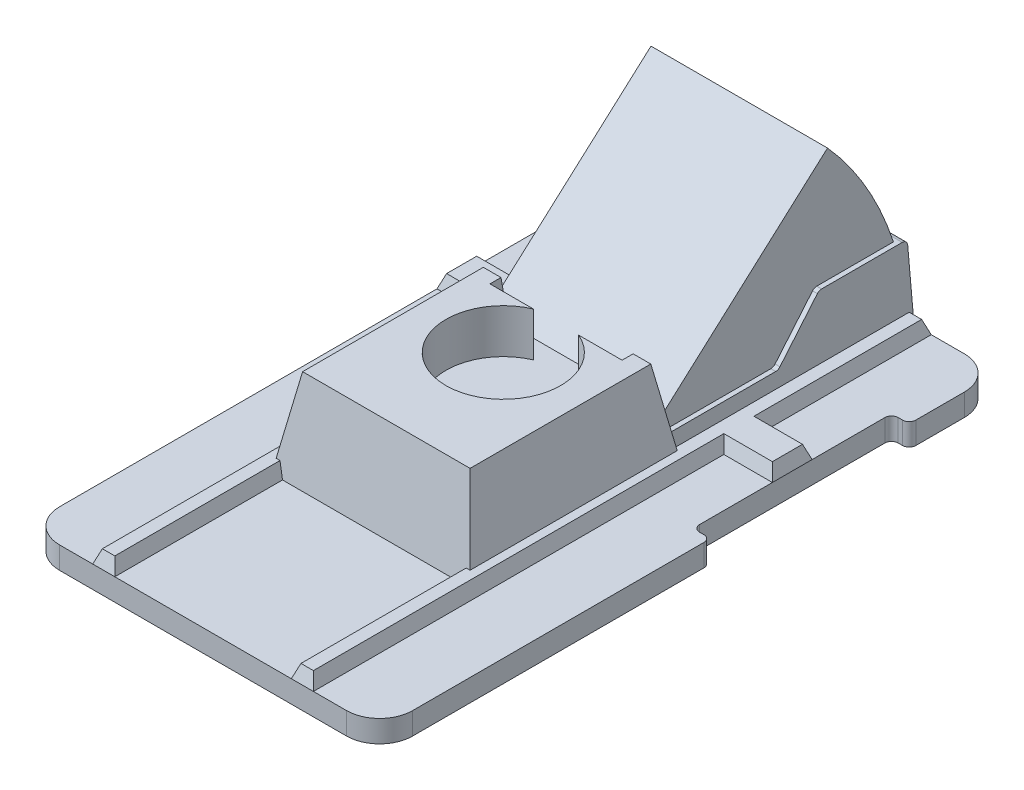
SolidWorks part; units mm, degrees
ref_plane "Front Plane" through (0, 0, 0) normal (0, 0, 1) x (1, 0, 0)
ref_plane "Top Plane" through (0, 0, 0) normal (0, 1, 0) x (1, 0, 0)
ref_plane "Right Plane" through (0, 0, 0) normal (1, 0, 0) x (0, 0, -1)
sketch "Sketch1" plane through (0, 0, 0) normal (0, 1, 0) x (1, 0, 0)
  line L0 (8, 10.3) -> (8, 12.5)
  line L1 (6.5, -14) -> (-6.5, -14)
  line L2 (8, -12.5) -> (8, 0.7)
  line L3 (6.5, 14) -> (-6.5, 14)
  line L4 (-8, -12.5) -> (-8, 12.5)
  line L5 (8, -14) -> (-8, 14) construction
  line L6 (8, 14) -> (-8, -14) construction
  line L7 (7.7, 10) -> (7.5, 10)
  line L9 (7.7, 1) -> (7.5, 1)
  line L10 (7.2, 9.7) -> (7.2, 1.3)
  arc A0 (-6.5, -14) -> (-8, -12.5) centre (-6.5, -12.5) cw
  arc A1 (6.5, -14) -> (8, -12.5) centre (6.5, -12.5) ccw
  arc A2 (8, 12.5) -> (6.5, 14) centre (6.5, 12.5) ccw
  arc A3 (-6.5, 14) -> (-8, 12.5) centre (-6.5, 12.5) ccw
  arc A4 (8, 0.7) -> (7.7, 1) centre (7.7, 0.7) ccw
  arc A5 (7.5, 1) -> (7.2, 1.3) centre (7.5, 1.3) cw
  arc A6 (7.7, 10) -> (8, 10.3) centre (7.7, 10.3) ccw
  arc A7 (7.5, 10) -> (7.2, 9.7) centre (7.5, 9.7) ccw
  point P0 (0, 0)
  point P24 (8, 1)
  point P27 (7.2, 1)
  point P30 (8, 10)
  point P33 (7.2, 10)
  dimension "D3" = 1.5
  dimension "D7" = 0.3
  dimension "D1" = 16
  dimension "D2" = 28
  dimension "D4" = 0.8
  dimension "D5" = 4
  dimension "D6" = 9
extrude "Boss-Extrude1" add sketch "Sketch1" along normal blind 1
sketch "Sketch2" plane through (0, 1, 0) normal (0, 1, 0) x (1, 0, 0)
  line L0 (-8, 12.5) -> (-8, -12.5) construction
  line L1 (-8, 4.6) -> (-5, 4.6)
  line L2 (-8, 4.6) -> (-8, 6.4)
  line L3 (-8, 6.4) -> (-5, 6.4)
  line L4 (7.2, 4.6) -> (7.2, 6.4)
  line L5 (-8, 4.6) -> (7.2, 6.4) construction
  line L6 (-8, 6.4) -> (7.2, 4.6) construction
  line L7 (7.2, 1.3) -> (7.2, 9.7) construction
  line L8 (6.5, 14) -> (-6.5, 14) construction
  line L9 (-6.5, -14) -> (6.5, -14) construction
  line L10 (-4, -14) -> (-5, -14)
  line L11 (-4, -14) -> (-4, 4.6)
  line L12 (-4, 14) -> (-5, 14)
  line L13 (-5, -14) -> (-5, 4.6)
  line L14 (-4, -14) -> (-5, 14) construction
  line L15 (-4, 14) -> (-5, -14) construction
  line L16 (5, -14) -> (4, -14)
  line L17 (5, -14) -> (5, 4.6)
  line L18 (5, 14) -> (4, 14)
  line L19 (4, -14) -> (4, 4.6)
  line L20 (5, -14) -> (4, 14) construction
  line L21 (5, 14) -> (4, -14) construction
  line L22 (-5, 6.4) -> (-5, 14)
  line L23 (-4, 6.4) -> (-4, 14)
  line L26 (4, 6.4) -> (4, 14)
  line L27 (5, 4.6) -> (7.2, 4.6)
  line L28 (5, 6.4) -> (5, 14)
  line L29 (5, 6.4) -> (7.2, 6.4)
  line L30 (-4, 6.4) -> (-4, 4.6)
  line L31 (4, 6.4) -> (4, 4.6)
  point P0 (-0.4, 5.5)
  point P9 (7.2, 5.5)
  point P10 (4.5, 0)
  point P13 (-4.5, 0)
  point P33 (-1.0138, 5.5)
  point P34 (-1.4145, 5.5)
  point P35 (0, 0)
  dimension "D1" = 7.6
  dimension "D2" = 10
  dimension "D3" = 8
  dimension "D4" = 1
  dimension "D5" = 5
extrude "Boss-Extrude2" add sketch "Sketch2" along normal blind 0.6 draft 20
sketch "Sketch4" plane through (0, 1, 0) normal (0, 1, 0) x (1, 0, 0)
  line L1 (4.5, -6.4) -> (-4.5, -6.4)
  line L2 (4.5, -6.4) -> (4.5, 3.2)
  line L3 (4.5, 3.2) -> (-4.5, 3.2)
  line L4 (-4.5, -6.4) -> (-4.5, 3.2)
  line L6 (-4, -14) -> (4, -14) construction
  line L7 (4, -14) -> (5, -14) construction
  line L8 (-5, -14) -> (-4, -14) construction
  point P10 (4.5, -14)
  point P11 (-4.5, -14)
  dimension "D1" = 7.6
  dimension "D2" = 9.6
extrude "Boss-Extrude3" add sketch "Sketch4" along normal blind 4 draft 10
sketch "Sketch5" plane through (0, 5, 0) normal (0, 1, 0) x (1, 0, 0)
  line L1 (3.7947, 2.4947) -> (-3.7947, -5.6947) construction
  line L2 (3.7947, 2.4947) -> (-3.7947, 2.4947) construction
  line L3 (3.7947, -5.6947) -> (-3.7947, 2.4947) construction
  line L4 (-2.9947, 1.9947) -> (-1.0251, 1.9947)
  line L5 (-2.9947, 1.9947) -> (-2.9947, 2.4947)
  line L6 (-2.9947, 2.4947) -> (2.9947, 2.4947) construction
  line L7 (2.9947, 1.9947) -> (2.9947, 2.4947)
  line L8 (-2.9947, 1.9947) -> (2.9947, 2.4947) construction
  line L9 (-2.9947, 2.4947) -> (2.9947, 1.9947) construction
  line L10 (3.7947, -5.6947) -> (3.7947, 2.4947) construction
  line L11 (-3.7947, -5.6947) -> (3.7947, -5.6947) construction
  line L12 (-1.0251, 1.9947) -> (1.0251, 1.9947) construction
  line L13 (1.0251, 1.9947) -> (2.9947, 1.9947)
  line L14 (4, 3.2) -> (-4, 3.2) construction
  line L15 (-2.9947, 2.4947) -> (2.9947, 2.4947) construction
  line L16 (-2.9947, 2.4947) -> (-2.9947, 3.2)
  line L17 (-2.9947, 3.2) -> (2.9947, 3.2)
  line L18 (2.9947, 2.4947) -> (2.9947, 3.2)
  arc A0 (-1.0251, 1.9947) -> (1.0251, 1.9947) centre (0, -0.3947) ccw
  arc A1 (1.0251, 1.9947) -> (-1.0251, 1.9947) centre (0, -0.3947) ccw construction
  point P10 (0, -1.6)
  point P11 (0, 2.2447)
  point P22 (-2.4947, 3.2)
  point P28 (2.4947, 3.2)
  dimension "D1" = 5.2
  dimension "D2" = 0.8
  dimension "D3" = 0.5
  dimension "D4" = 5.3
extrude "Cut-Extrude1" cut sketch "Sketch5" against normal blind 2
sketch "Sketch6" plane through (0, 0, 0) normal (1, 0, 0) x (0, 0, -1)
  line L0 (1.9947, 5) -> (-2.9947, 5) construction
  line L1 (1.9947, 5) -> (-2.9947, 5) construction
  line L2 (-0.5, 5) -> (-0.5, 0) construction
  line L3 (-12.5, 0) -> (0.7, 0) construction
  line L4 (-0.5, 0) -> (10.298, 9.6775)
  line L5 (14, 0) -> (-0.5, 0)
  line L6 (2.4947, 5) -> (2.8473, 3) construction
  line L7 (2.4947, 5) -> (2.8473, 3) construction
  arc A0 (14, 0) -> (10.298, 9.6775) centre (-0.5, 0) ccw
  point P2 (-0.5, 5)
  point P12 (10.8294, 9.0495)
extrude "Boss-Extrude4" add sketch "Sketch6" along normal up to vertex (4 mm away) and the other way up to vertex (4 mm away)
sketch "Sketch7" plane through (0, 0, 0) normal (1, 0, 0) x (0, 0, -1)
  line L0 (2.9708, 2.3) -> (7.7313, 2.3)
  line L1 (2.4947, 5) -> (3.0942, 1.6) construction
  line L2 (7.9227, 2.3893) -> (9.6189, 4.4107)
  line L3 (9.8103, 4.5) -> (13.4648, 4.5)
  line L4 (13.7137, 4.2719) -> (14, 1)
  line L5 (14, 1) -> (3.2, 1)
  line L6 (1.3, 1) -> (4.6, 1) construction
  line L7 (3.2, 1) -> (2.9708, 2.3)
  line L8 (3.2, 1) -> (2.8473, 3) construction
  arc A0 (7.7313, 2.3) -> (7.9227, 2.3893) centre (7.7313, 2.5499) ccw
  arc A1 (9.6189, 4.4107) -> (9.8103, 4.5) centre (9.8103, 4.2501) cw
  arc A2 (13.4648, 4.5) -> (13.7137, 4.2719) centre (13.4648, 4.2501) cw
  point P13 (14.5118, 4.5)
  point P18 (9.6938, 4.5)
  point P21 (13.6938, 4.5)
  dimension "D6" = 0.2499
  dimension "D1" = 4
  dimension "D2" = 1.3
  dimension "D3" = 3.5
  dimension "D4" = 50
  dimension "D5" = 85
extrude "Boss-Extrude5" add sketch "Sketch7" along normal up to vertex (4.2184 mm away) and the other way up to vertex (4.2184 mm away)
sketch "Sketch9" plane through (0, 0, 0) normal (1, 0, 0) x (0, 0, -1)
  line L0 (14, 1) -> (14, 0) construction
  line L1 (12.4, 0) -> (-5.6, 0)
  line L2 (12.4, 0) -> (12.4, 1.6)
  line L3 (6.2965, 1.6) -> (-1.5554, 1.6)
  line L4 (-5.6, 0) -> (-5.6, 1.5781)
  line L5 (12.5, 0) -> (14, 0) construction
  line L6 (-5.2493, 2.4) -> (-2.5624, 2.4)
  line L7 (-2.3858, 2.3268) -> (-1.7321, 1.6732)
  line L8 (-5.4953, 2.1935) -> (-5.5962, 1.6215)
  line L9 (-5.6947, 5) -> (-6.2942, 1.6) construction
  line L10 (-5.6947, 5) -> (-6.2942, 1.6)
  line L11 (6.4732, 1.6732) -> (9.2268, 4.4268)
  line L12 (9.4035, 4.5) -> (11.822, 4.5)
  line L18 (10.298, 9.6775) -> (2.8473, 3) construction
  line L19 (10.298, 9.6775) -> (2.8473, 3) construction
  line L20 (12.4, 1.6) -> (6.4, 1.6) construction
  line L21 (-1.6589, 1.6) -> (-5.6, 1.6) construction
  arc A0 (12.4, 1.6) -> (12.0643, 4.3111) centre (1.2853, 1.6) ccw
  arc A1 (-5.5962, 1.6215) -> (-5.6, 1.5781) centre (-5.3501, 1.5781) ccw
  arc A2 (-2.5624, 2.4) -> (-2.3858, 2.3268) centre (-2.5624, 2.1501) cw
  arc A3 (-5.2493, 2.4) -> (-5.4953, 2.1935) centre (-5.2493, 2.1501) ccw
  arc A4 (-1.7321, 1.6732) -> (-1.5554, 1.6) centre (-1.5554, 1.8499) ccw
  arc A5 (6.4732, 1.6732) -> (6.2965, 1.6) centre (6.2965, 1.8499) cw
  arc A6 (11.822, 4.5) -> (12.0643, 4.3111) centre (11.822, 4.2501) cw
  arc A7 (9.2268, 4.4268) -> (9.4035, 4.5) centre (9.4035, 4.2501) cw
  point P19 (1.2853, 1.6)
  point P20 (0, 0)
  point P21 (0, 0)
  point P27 (-2.4589, 2.4)
  point P30 (-5.4589, 2.4)
  dimension "D10" = 0.2499
  dimension "D1" = 18
  dimension "D2" = 1.6
  dimension "D3" = 1.6
  dimension "D4" = 3
  dimension "D5" = 45
  dimension "D6" = 0.8
  dimension "D7" = 45
  dimension "D8" = 4.5
  dimension "D9" = 6
extrude "Cut-Extrude2" cut sketch "Sketch9" against normal blind 3 and the other way blind 3 contours A7 L11 A5 L3 A4 L7 A2 L6 A3 L8 A1 L4 L1 L2 A0 A6 L12
